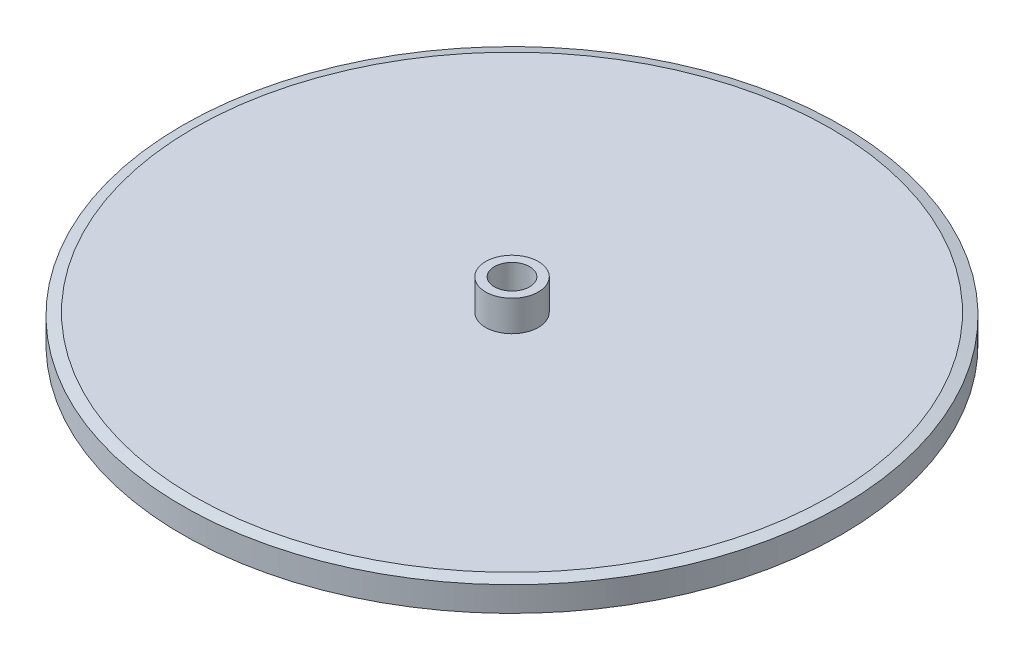
SolidWorks part; units mm, degrees
material "Сталь ШХ15 ГОСТ 801-78"
ref_plane "Plane1" through (0, 0, 0) normal (0, 0, 1) x (1, 0, 0)
ref_plane "Plane2" through (0, 0, 0) normal (0, 1, 0) x (1, 0, 0)
ref_plane "Plane3" through (0, 0, 0) normal (1, 0, 0) x (0, 0, -1)
sketch "Эскиз1" plane through (0, 0, 0) normal (0, 0, 1) x (1, 0, 0)
  line L0 (0, 0) -> (37.5, 0)
  line L1 (37.5, 0) -> (37.5, 3.5)
  line L2 (37.5, 3.5) -> (3, 3.5)
  line L3 (3, 3.5) -> (3, 7)
  line L4 (3, 7) -> (0, 7)
  line L5 (0, 7) -> (0, 0)
  dimension "D1" = 3.5
  dimension "30" = 37.5
  dimension "D3" = 3
  dimension "D4" = 3.5
ref_axis "Ось1" through (0, 7, 0) along (0, -1, 0)
revolve "Повернуть2" add sketch "Эскиз1" angle 360 about axis through (0, 7, 0) along (0, -1, 0)
chamfer "Фаска1" distance 1.25 angle 15 1 edges at (-37.5, 3.5, 0)
sketch "Эскиз2" plane through (0, 0, 0) normal (0, -1, 0) x (-1, 0, 0)
  circle A0 centre (0, 0) radius 2
  dimension "D1" = 4
extrude "Вырез-Вытянуть3" cut sketch "Эскиз2" against normal through all both
chamfer "Фаска2" distance 1.25 angle 15 1 edges at (-37.5, 0, 0)
